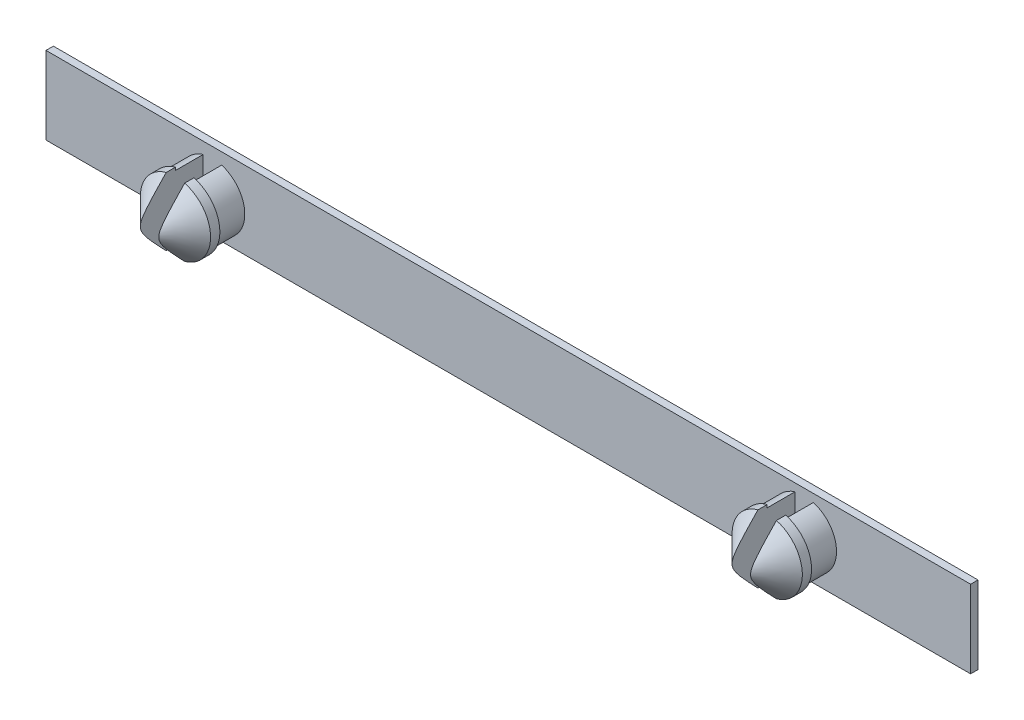
SolidWorks part; units mm, degrees
ref_plane "Přední rovina" through (0, 0, 0) normal (0, 0, 1) x (1, 0, 0)
ref_plane "Horní rovina" through (0, 0, 0) normal (0, 1, 0) x (1, 0, 0)
ref_plane "Pravá rovina" through (0, 0, 0) normal (1, 0, 0) x (0, 0, -1)
sketch "Skica2" plane through (0, 0, 0) normal (0, 0, 1) x (1, 0, 0)
  line L1 (-25, 2.1) -> (25, 2.1)
  line L2 (-25, 2.1) -> (-25, -2.1)
  line L3 (-25, -2.1) -> (25, -2.1)
  line L4 (25, 2.1) -> (25, -2.1)
  line L5 (-25, 2.1) -> (25, -2.1) construction
  line L6 (-25, -2.1) -> (25, 2.1) construction
  point P0 (0, 0)
  point P5 (-1, -0.2)
  dimension "D1" = 4.2
  dimension "D2" = 50
extrude "Přidat vysunutím2" add sketch "Skica2" along normal blind 0.4
sketch "Skica3" plane through (0, 0, 0.4) normal (0, 0, 1) x (1, 0, 0)
  line L0 (-25, 2.1) -> (-25, -2.1) construction
  line L1 (25, -2.1) -> (25, 2.1) construction
  line L2 (25, 2.1) -> (-25, 2.1) construction
  line L3 (-25, -2.1) -> (25, -2.1) construction
  circle A0 centre (-16, -0.2) radius 1.75
  circle A1 centre (16, 0) radius 1.75
  dimension "D1" = 3.5
  dimension "D3" = 3.5
  dimension "D2" = 9
  dimension "D4" = 9
  dimension "D5" = 2.3
  dimension "D6" = 1.9
extrude "Přidat vysunutím3" add sketch "Skica3" along normal blind 1.5
sketch "Skica5" plane through (0, 0, 1.9) normal (0, 0, 1) x (1, 0, 0)
  circle A0 centre (-16, -0.2) radius 1.9
  circle A1 centre (16, 0) radius 1.9
  dimension "D1" = 3.8
  dimension "D2" = 3.8
extrude "Přidat vysunutím5" add sketch "Skica5" along normal blind 2
chamfer "Zkosení2" distance 1.5 angle 45 2 edges at (17.9, 0, 3.9) (-14.1, -0.2, 3.9)
sketch "Skica7" plane through (0, 0, 3.9) normal (0, 0, 1) x (1, 0, 0)
  line L1 (-15.5, 2.3) -> (-16.5, 2.3)
  line L2 (-15.5, 2.3) -> (-15.5, -2.7)
  line L3 (-15.5, -2.7) -> (-16.5, -2.7)
  line L4 (-16.5, 2.3) -> (-16.5, -2.7)
  line L5 (-15.5, 2.3) -> (-16.5, -2.7) construction
  line L6 (-15.5, -2.7) -> (-16.5, 2.3) construction
  line L7 (15.5, 2.5) -> (16.5, 2.5)
  line L8 (15.5, 2.5) -> (15.5, -2.5)
  line L9 (15.5, -2.5) -> (16.5, -2.5)
  line L10 (16.5, 2.5) -> (16.5, -2.5)
  line L11 (15.5, 2.5) -> (16.5, -2.5) construction
  line L12 (15.5, -2.5) -> (16.5, 2.5) construction
  point P0 (-16, -0.2)
  point P5 (16, 0)
  dimension "D1" = 5
  dimension "D2" = 1
  dimension "D3" = 5
  dimension "D4" = 1
extrude "Odebrat vysunutím1" cut sketch "Skica7" against normal blind 3.5
equation "\"1.5.000mm\"=10"
